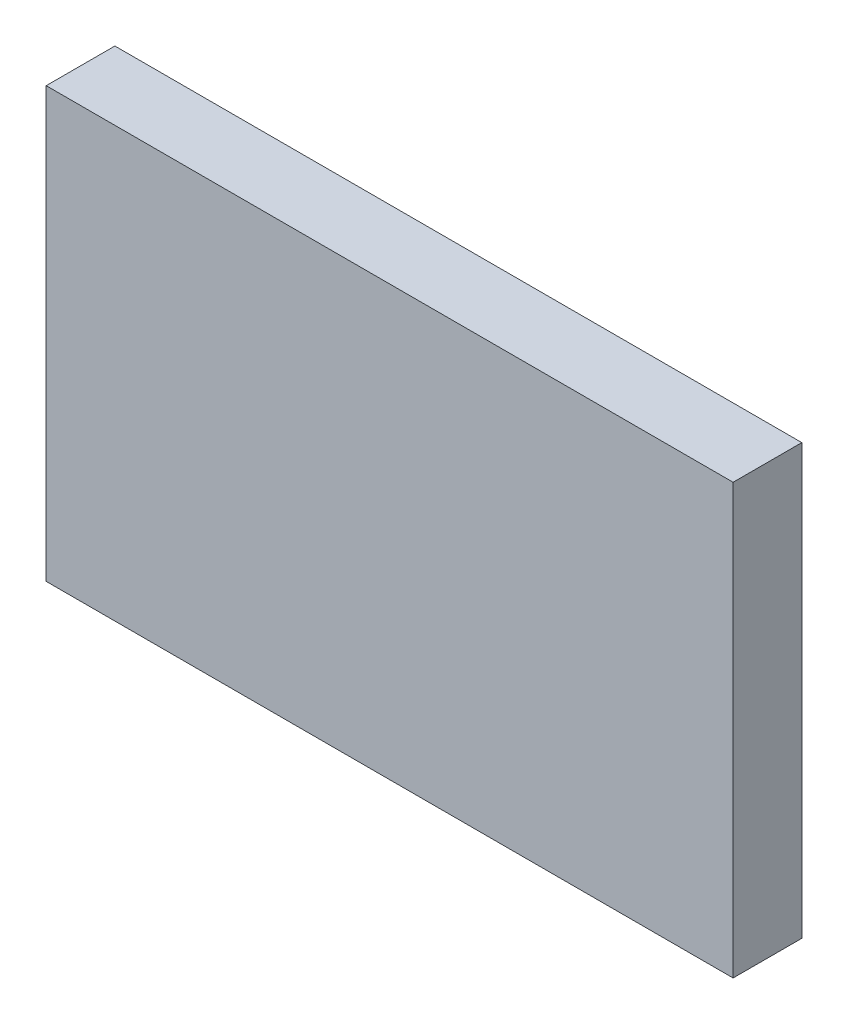
SolidWorks part; units mm, degrees
ref_plane "前视基准面" through (0, 0, 0) normal (0, 0, 1) x (1, 0, 0)
ref_plane "上视基准面" through (0, 0, 0) normal (0, 1, 0) x (1, 0, 0)
ref_plane "右视基准面" through (0, 0, 0) normal (1, 0, 0) x (0, 0, -1)
sketch "草图1" plane through (0, 0, 0) normal (0, 0, 1) x (1, 0, 0)
  line L1 (40, -25) -> (-40, -25)
  line L2 (40, -25) -> (40, 25)
  line L3 (40, 25) -> (-40, 25)
  line L4 (-40, -25) -> (-40, 25)
  line L5 (40, -25) -> (-40, 25) construction
  line L6 (40, 25) -> (-40, -25) construction
  point P0 (0, 0)
  dimension "D1" = 80
  dimension "D2" = 50
extrude "凸台-拉伸1" add sketch "草图1" along normal blind 8
